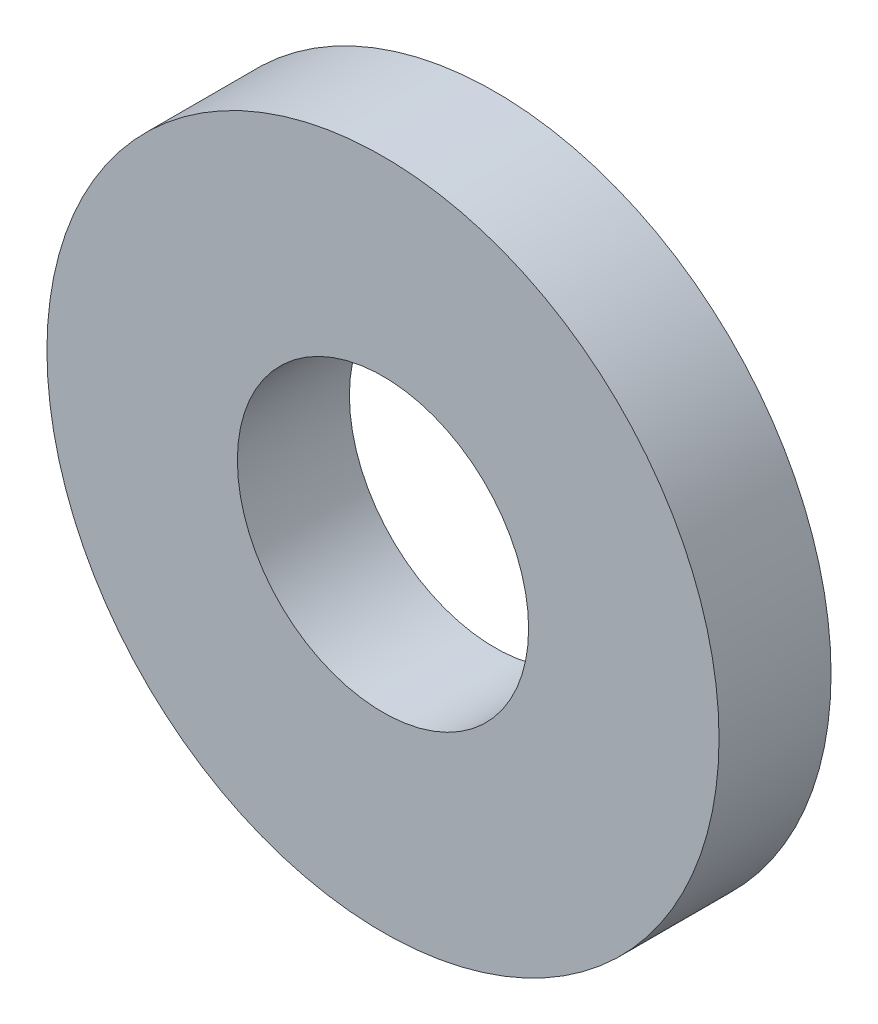
SolidWorks part; units mm, degrees
ref_plane "Front Plane" through (0, 0, 0) normal (0, 0, 1) x (1, 0, 0)
ref_plane "Top Plane" through (0, 0, 0) normal (0, 1, 0) x (1, 0, 0)
ref_plane "Right Plane" through (0, 0, 0) normal (1, 0, 0) x (0, 0, -1)
sketch "Sketch1" plane through (0, 0, 0) normal (0, 0, 1) x (1, 0, 0)
  circle A0 centre (0, 0) radius 2.6
  circle A1 centre (0, 0) radius 6
  dimension "D1" = 5.2
  dimension "D2" = 12
extrude "Boss-Extrude1" add sketch "Sketch1" along normal blind 2
